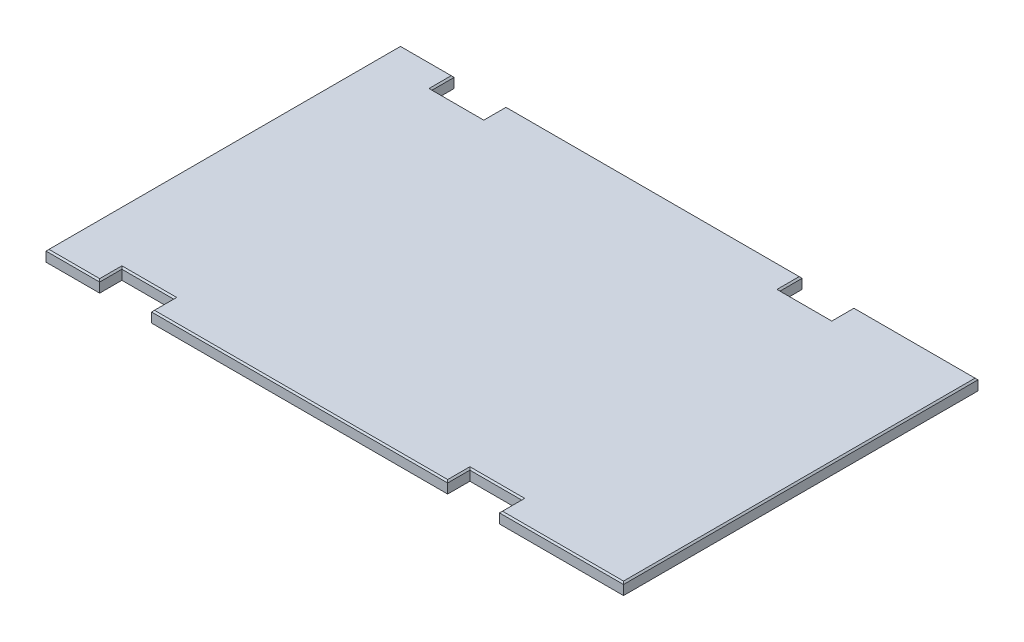
SolidWorks part; units mm, degrees
material "Oak"
ref_plane "Front Plane" through (0, 0, 0) normal (0, 0, 1) x (1, 0, 0)
ref_plane "Top Plane" through (0, 0, 0) normal (0, 1, 0) x (1, 0, 0)
ref_plane "Right Plane" through (0, 0, 0) normal (1, 0, 0) x (0, 0, -1)
sketch "Sketch1" plane through (0, 0, 0) normal (0, 1, 0) x (1, 0, 0)
  line L1 (0, 0) -> (990.6, 0)
  line L2 (0, 0) -> (0, 608.0125)
  line L3 (0, 608.0125) -> (990.6, 608.0125)
  line L4 (990.6, 0) -> (990.6, 608.0125)
  dimension "D1" = 608.0125
  dimension "D2" = 990.6
extrude "Boss-Extrude1" add sketch "Sketch1" along normal blind 19.05
sketch "Sketch2" plane through (0, 19.05, 0) normal (0, 1, 0) x (1, 0, 0)
  line L0 (-127.9594, 304.0062) -> (1156.0653, 304.0062) construction
  line L1 (777.875, 569.9125) -> (688.975, 569.9125)
  line L2 (777.875, 569.9125) -> (777.875, 608.0125)
  line L3 (777.875, 608.0125) -> (688.975, 608.0125)
  line L4 (688.975, 569.9125) -> (688.975, 608.0125)
  line L5 (0, 0) -> (990.6, 0) construction
  line L6 (92.075, 608.0125) -> (180.975, 608.0125)
  line L7 (92.075, 608.0125) -> (92.075, 569.9125)
  line L8 (92.075, 569.9125) -> (180.975, 569.9125)
  line L9 (180.975, 608.0125) -> (180.975, 569.9125)
  line L10 (0, 608.0125) -> (0, 0) construction
  line L11 (180.975, 0) -> (180.975, 38.1)
  line L12 (990.6, 608.0125) -> (0, 608.0125) construction
  line L13 (92.075, 38.1) -> (180.975, 38.1)
  line L14 (92.075, 0) -> (92.075, 38.1)
  line L15 (92.075, 0) -> (180.975, 0)
  line L16 (688.975, 38.1) -> (688.975, 0)
  line L17 (777.875, 0) -> (688.975, 0)
  line L18 (777.875, 38.1) -> (777.875, 0)
  line L19 (777.875, 38.1) -> (688.975, 38.1)
  dimension "D1" = 92.075
  dimension "D2" = 88.9
  dimension "D3" = 688.975
  dimension "D4" = 88.9
  dimension "D5" = 38.1
extrude "Cut-Extrude1" cut sketch "Sketch2" against normal through all
chamfer "Chamfer1" distance 2.54 angle 45 20 edges at (990.6, 19.05, -304.0062) (884.2375, 19.05, 0) (46.0375, 19.05, 0) (0, 19.05, -304.0062) (46.0375, 19.05, -608.0125) (92.075, 19.05, -588.9625) (136.525, 19.05, -569.9125) (180.975, 19.05, -588.9625) (434.975, 19.05, -608.0125) (688.975, 19.05, -588.9625) (733.425, 19.05, -569.9125) (777.875, 19.05, -588.9625) (884.2375, 19.05, -608.0125) (688.975, 19.05, -19.05) (434.975, 19.05, 0) (180.975, 19.05, -19.05) (136.525, 19.05, -38.1) (92.075, 19.05, -19.05) (777.875, 19.05, -19.05) (733.425, 19.05, -38.1)
